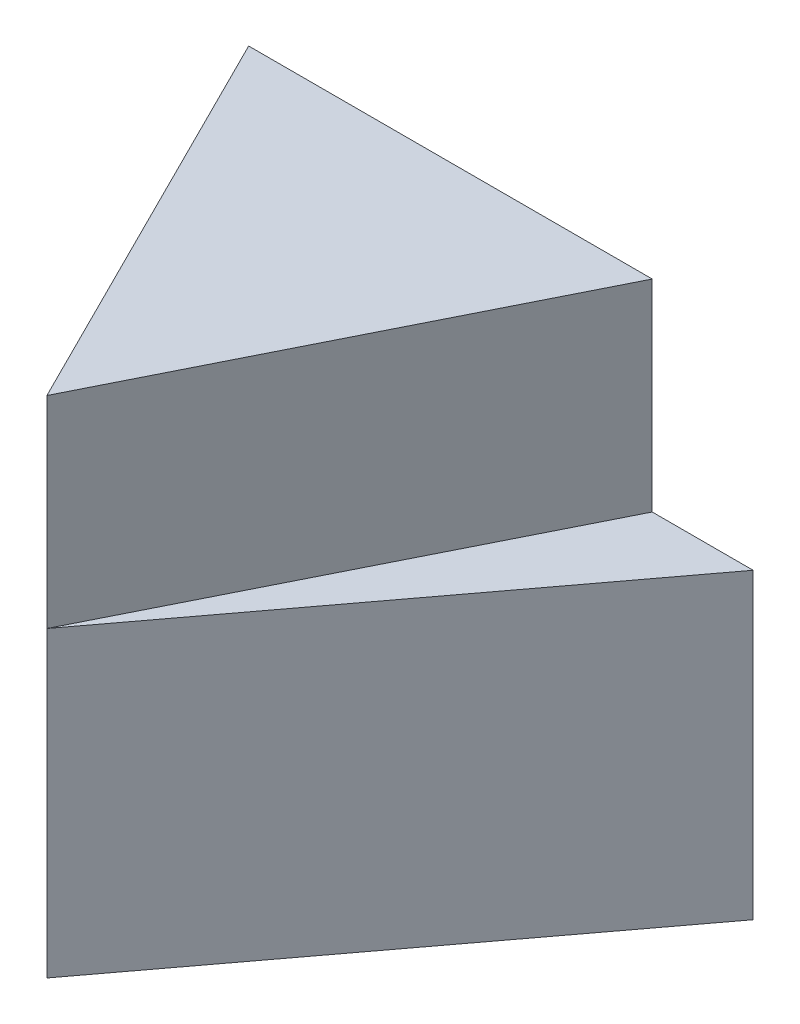
SolidWorks part; units mm, degrees
ref_plane "Front Plane" through (0, 0, 0) normal (0, 0, 1) x (1, 0, 0)
ref_plane "Top Plane" through (0, 0, 0) normal (0, 1, 0) x (1, 0, 0)
ref_plane "Right Plane" through (0, 0, 0) normal (1, 0, 0) x (0, 0, -1)
sketch "Sketch1" plane through (0, 0, 0) normal (0, 1, 0) x (1, 0, 0)
  line L0 (0, 0) -> (-3, 4)
  line L1 (-3, 4) -> (3, 4)
  line L2 (3, 4) -> (0, 0)
  dimension "D1" = 6
  dimension "D2" = 3
  dimension "D3" = 4
extrude "Boss-Extrude1" add sketch "Sketch1" along normal blind 3
sketch "Sketch2" plane through (0, 3, 0) normal (0, 1, 0) x (1, 0, 0)
  line L0 (0, 0) -> (-2, 4)
  line L1 (3, 4) -> (-3, 4) construction
  line L2 (-2, 4) -> (2, 4)
  line L3 (2, 4) -> (0, 0)
  dimension "D1" = 4
  dimension "D2" = 2
extrude "Boss-Extrude2" add sketch "Sketch2" along normal blind 2
